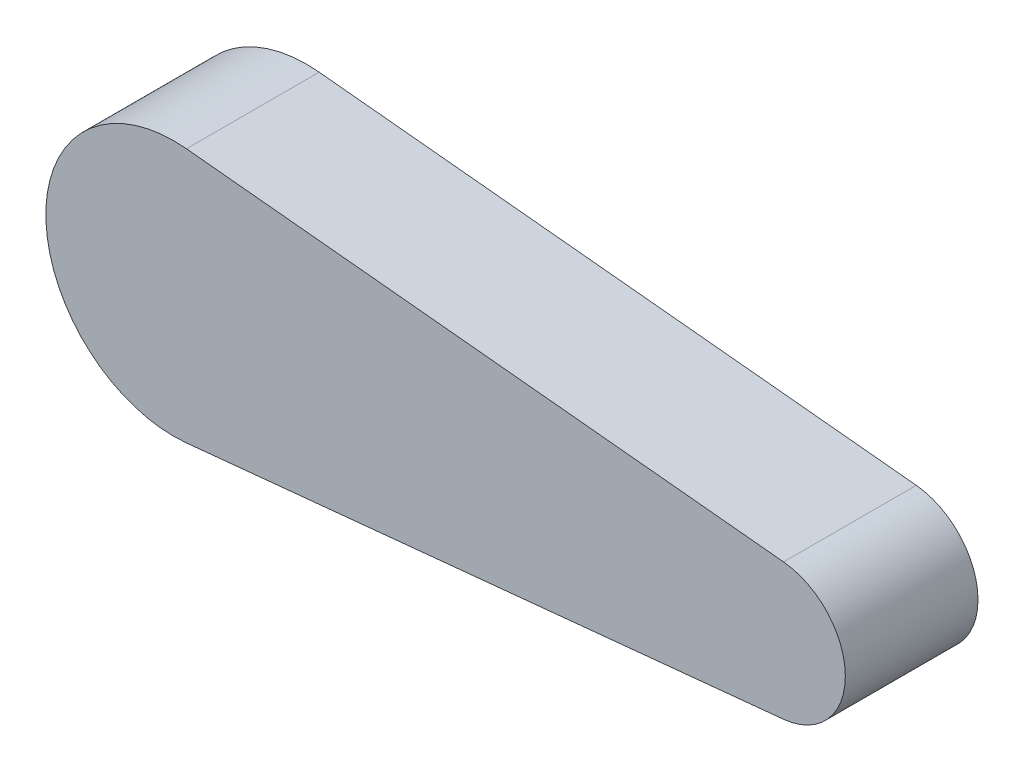
SolidWorks part; units mm, degrees
material "ABS"
ref_plane "Plan de face" through (0, 0, 0) normal (0, 0, 1) x (1, 0, 0)
ref_plane "Plan de dessus" through (0, 0, 0) normal (0, 1, 0) x (1, 0, 0)
ref_plane "Plan de droite" through (0, 0, 0) normal (1, 0, 0) x (0, 0, -1)
sketch "Esquisse1" plane through (0, 0, 0) normal (0, 0, 1) x (1, 0, 0)
  line L0 (0.27, 0) -> (50.27, 0) construction
  line L1 (10.5995, 9.6) -> (55.5995, 5.1357)
  line L2 (10.5995, -9.6) -> (55.5995, -5.1357)
  arc A0 (10.5995, 9.6) -> (10.5995, -9.6) centre (9.6471, 0) ccw
  arc A1 (55.5995, 5.1357) -> (55.5995, -5.1357) centre (55.09, 0) cw
  dimension "D1" = 9.6
  dimension "D2" = 50
  dimension "D3" = 5.1357
  dimension "D4" = 45
extrude "Boss.-Extru.1" add sketch "Esquisse1" along normal blind 10
sketch "Sketch1" plane through (0, 0, 0) normal (0, 0, -1) x (-1, 0, 0)
  line L0 (0, 0) -> (-60.2509, 0) construction
  line L1 (-10.5995, 9.6) -> (-10.5995, -9.6) construction
  arc A0 (-55.5995, 5.1357) -> (-55.5995, -5.1357) centre (-55.09, 0) ccw construction
  circle A1 centre (-10.5995, 0) radius 3.55
  dimension "D1" = 7.1
extrude "Cut-Extrude1" cut sketch "Sketch1" against normal blind 8
